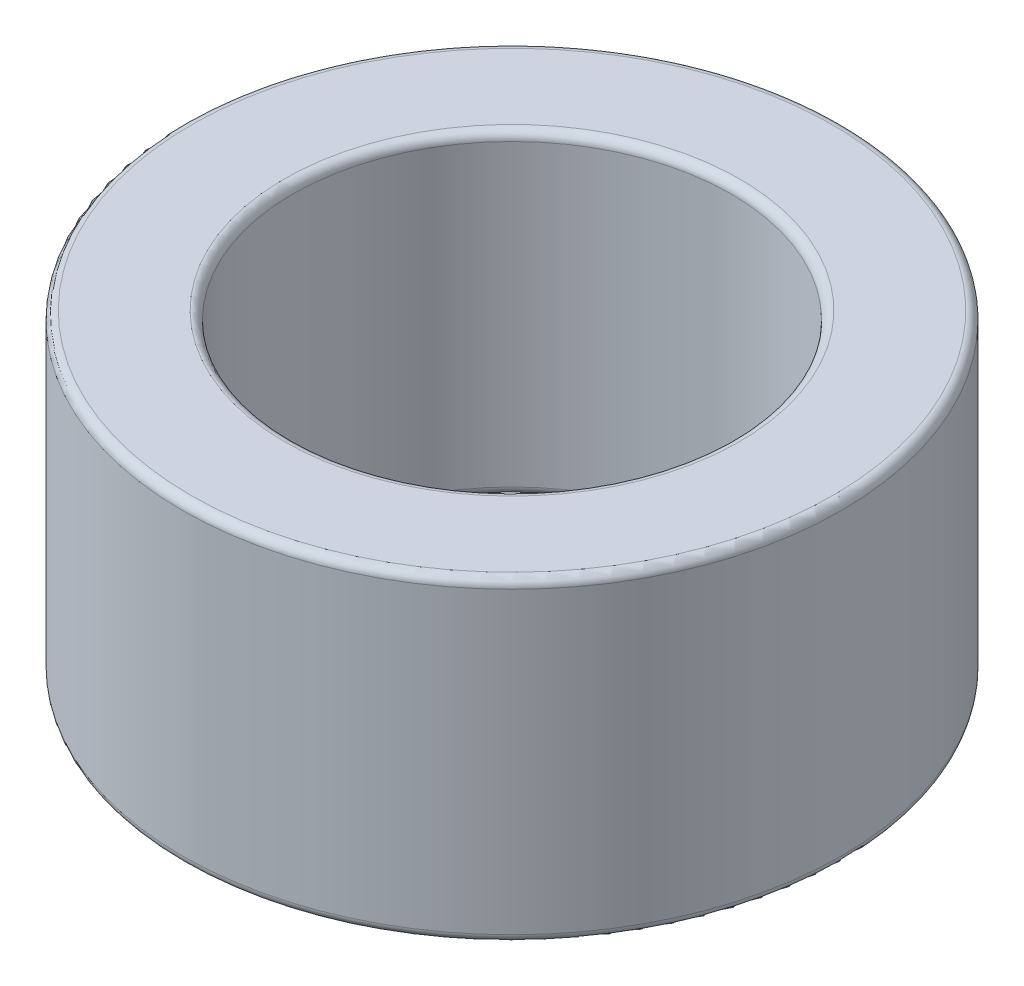
SolidWorks part; units mm, degrees
material "Полиамид ПА-6Б ТУ 6-05-988-93"
ref_plane "Спереди" through (0, 0, 0) normal (0, 0, 1) x (1, 0, 0)
ref_plane "Сверху" through (0, 0, 0) normal (0, 1, 0) x (1, 0, 0)
ref_plane "Справа" through (0, 0, 0) normal (1, 0, 0) x (0, 0, -1)
sketch "Эскиз1" plane through (0, 0, 0) normal (0, 1, 0) x (1, 0, 0)
  circle A0 centre (0, 0) radius 3.8
  circle A1 centre (0, 0) radius 2.525
  dimension "D1" = 7.6
  dimension "D2" = 5.05
extrude "Бобышка-Вытянуть1" add sketch "Эскиз1" along normal blind 3.65
fillet "Скругление1" radius 0.1 4 edges at (0, 0, 2.525) (0, 0, 3.8) (0, 3.65, 2.525) (0, 3.65, 3.8)
